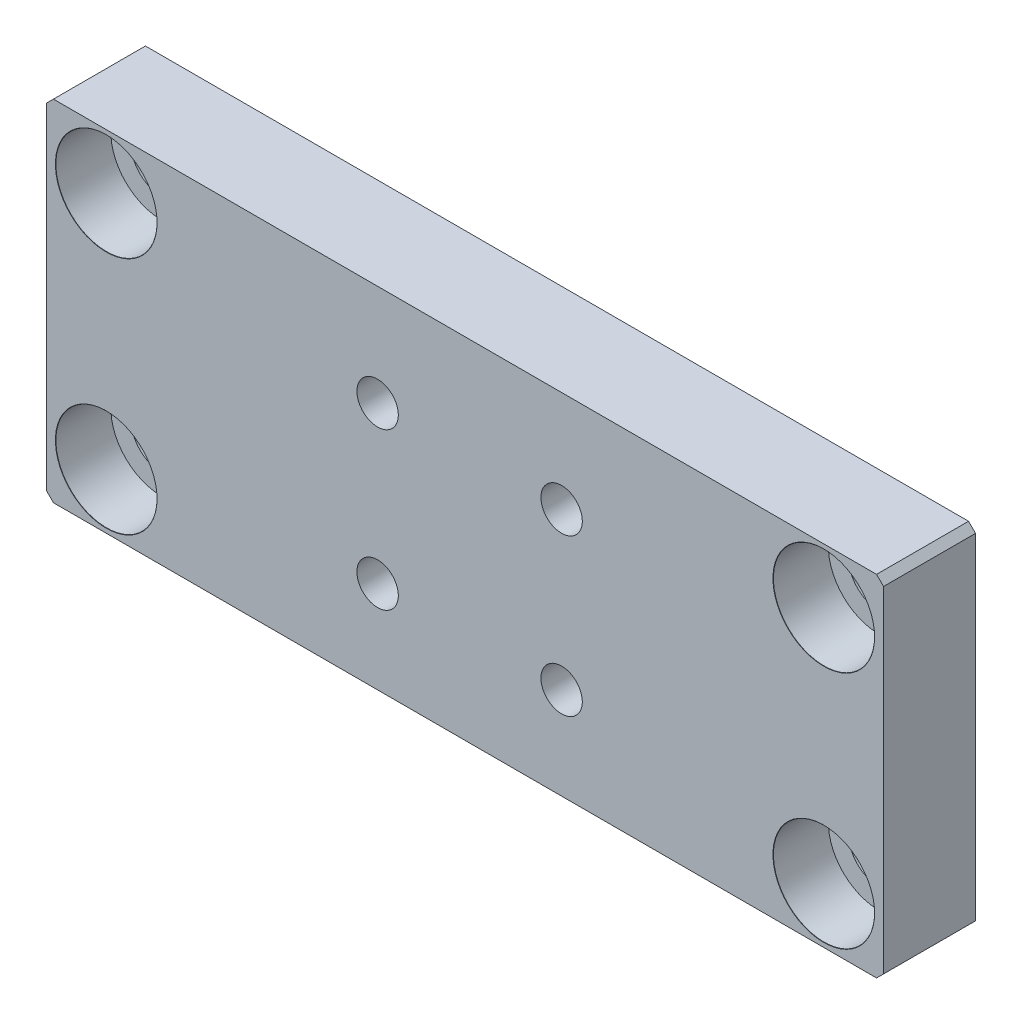
SolidWorks part; units mm, degrees
ref_plane "Front Plane" through (0, 0, 0) normal (0, 0, 1) x (1, 0, 0)
ref_plane "Top Plane" through (0, 0, 0) normal (0, 1, 0) x (1, 0, 0)
ref_plane "Right Plane" through (0, 0, 0) normal (1, 0, 0) x (0, 0, -1)
sketch "Sketch1" plane through (0, 0, 0) normal (0, 0, 1) x (1, 0, 0)
  line B0 (92, 39.24) -> (91.24, 40)
  line B1 (91.24, 40) -> (1.76, 40)
  line B2 (1.76, 40) -> (1, 39.24)
  line B3 (1, 39.24) -> (1, 2.76)
  line B4 (1, 2.76) -> (1.76, 2)
  line B5 (1.76, 2) -> (91.24, 2)
  line B6 (91.24, 2) -> (92, 2.76)
  line B7 (92, 2.76) -> (92, 39.24)
sketch_block_instance "Block-Mounting plate-1"
sketch_block "Block-Mounting plate"
extrude "Boss-Extrude1" add sketch "Sketch1" along normal blind 10
hole_wizard "CBORE for M6 SHCS1" positions "Sketch3" profile "Sketch4" counterbore size "M6" standard "ANSI Metric" end condition through all
sketch "Sketch3" plane through (0, 0, 10) normal (0, 0, 1) x (1, 0, 0)
  line L0 (1, 39.24) -> (1, 2.76) construction
  line L1 (91.24, 40) -> (1.76, 40) construction
  point P0 (7.5, 34)
  dimension "D1" = 6.5
  dimension "D2" = 6
sketch "Sketch4" plane through (7.5, 34, 10) normal (1, 0, 0) x (0, -1, 0)
  line L0 (0, 0) -> (0, 10)
  line L1 (0, 10) -> (3.3, 10)
  line L3 (3.3, 10) -> (3.3, 6)
  line L4 (5.5, 6) -> (3.3, 6)
  line L5 (5.5, 6) -> (5.5, 0.025)
  line L6 (5.5, 0.025) -> (5.525, 0)
  line L7 (5.525, 0) -> (0, 0)
  line L8 (-5.5, 0.025) -> (-5.525, 0) construction
  line L11 (0, -6.35) -> (0, 107.95) construction
  dimension "Thru Hole Dia." = 6.6
  dimension "Thru Hole Depth" = 10
  dimension "C'Bore Dia." = 11
  dimension "C'Bore Depth" = 6
  dimension "Near C'Sink Dia." = 11.05
  dimension "Near C'Sink Angle" = 90
pattern_linear "LPattern2" count 2 spacing 78 along (1, 0, 0) count 2 spacing 26 along (0, -1, 0) of "CBORE for M6 SHCS1"
hole_wizard "CBORE for M4 SHCS1" positions "Sketch5" profile "Sketch6" counterbore size "M4" standard "ANSI Metric" end condition through all
sketch "Sketch5" plane through (0, 0, 0) normal (0, 0, -1) x (-1, 0, 0)
  line L0 (-92, 2.76) -> (-92, 39.24) construction
  line L4 (-1.76, 2) -> (-91.24, 2) construction
  point P0 (-57, 12)
  point P17 (0, 0)
  point P18 (0, 0)
  dimension "D1" = 35
  dimension "D2" = 10
sketch "Sketch6" plane through (57, 12, 0) normal (1, 0, 0) x (0, 1, 0)
  line L0 (0, 0) -> (0, 10)
  line L1 (0, 10) -> (2.25, 10)
  line L3 (2.25, 10) -> (2.25, 4)
  line L4 (4, 4) -> (2.25, 4)
  line L5 (4, 4) -> (4, 0.025)
  line L6 (4, 0.025) -> (4.025, 0)
  line L7 (4.025, 0) -> (0, 0)
  line L8 (-4, 0.025) -> (-4.025, 0) construction
  line L11 (0, -6.35) -> (0, 107.95) construction
  dimension "Thru Hole Dia." = 4.5
  dimension "Thru Hole Depth" = 10
  dimension "C'Bore Dia." = 8
  dimension "C'Bore Depth" = 4
  dimension "Near C'Sink Dia." = 8.05
  dimension "Near C'Sink Angle" = 90
pattern_linear "LPattern3" count 2 spacing 20 along (-1, 0, 0) count 2 spacing 17 along (0, 1, 0) of "CBORE for M4 SHCS1"
